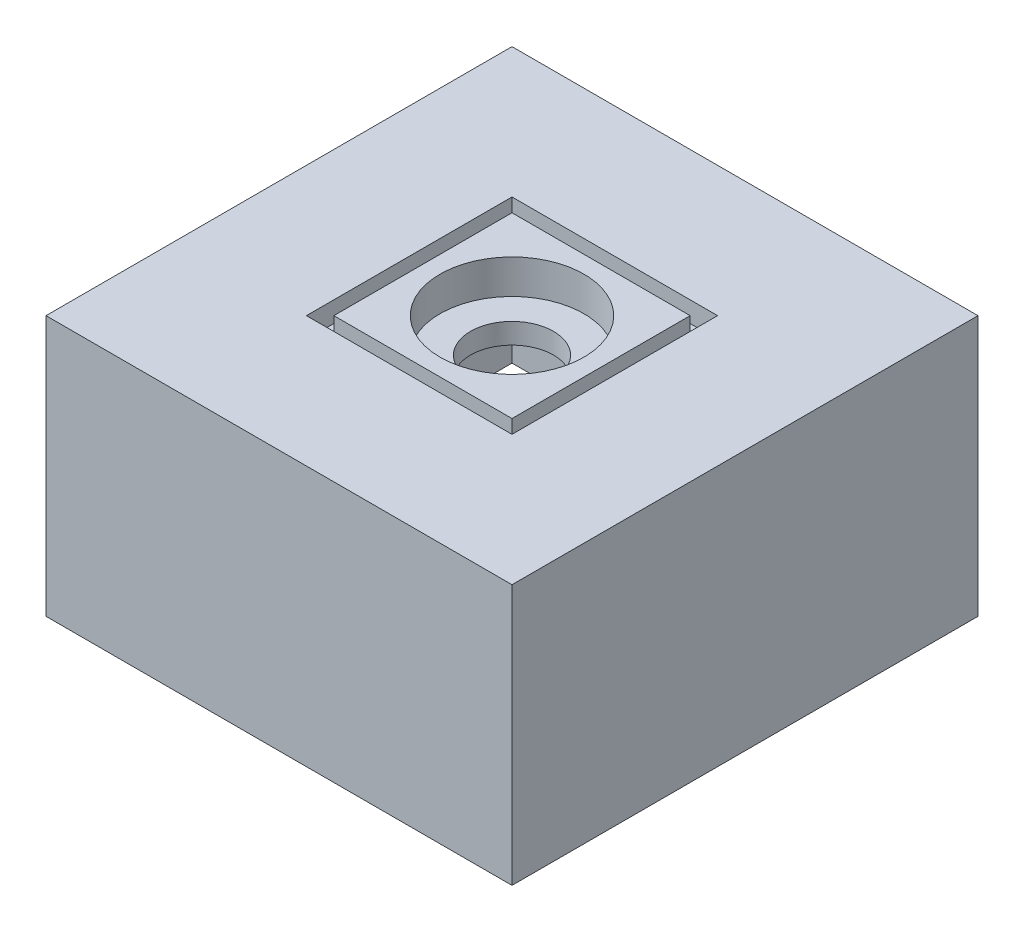
SolidWorks part; units mm, degrees
ref_plane "Front Plane" through (0, 0, 0) normal (0, 0, 1) x (1, 0, 0)
ref_plane "Top Plane" through (0, 0, 0) normal (0, 1, 0) x (1, 0, 0)
ref_plane "Right Plane" through (0, 0, 0) normal (1, 0, 0) x (0, 0, -1)
sketch "Sketch2" plane through (0, 0, 0) normal (0, 1, 0) x (1, 0, 0)
  line L1 (0, 0) -> (68, 0)
  line L2 (0, 0) -> (0, -68)
  line L3 (0, -68) -> (68, -68)
  line L4 (68, 0) -> (68, -68)
  dimension "D1" = 68
  dimension "D2" = 68
extrude "Boss-Extrude1" add sketch "Sketch2" along normal blind 38
sketch "Sketch3" plane through (0, 0, 0) normal (0, -1, 0) x (1, 0, 0)
  line L0 (0, 68) -> (68, 68) construction
  line L1 (2, 66) -> (66, 66)
  line L2 (2, 66) -> (2, 2)
  line L3 (2, 2) -> (66, 2)
  line L4 (66, 66) -> (66, 2)
  line L5 (0, 0) -> (0, 68) construction
  dimension "D1" = 64
  dimension "D2" = 2
  dimension "D3" = 2
extrude "Cut-Extrude1" cut sketch "Sketch3" against normal blind 30
sketch "Sketch5" plane through (0, 38, 0) normal (0, 1, 0) x (1, 0, 0)
  line L0 (0, 0) -> (68, -68) construction
  line L1 (0, -68) -> (68, 0) construction
  line L3 (19, -19) -> (49, -19)
  line L4 (19, -19) -> (19, -49)
  line L5 (19, -49) -> (49, -49)
  line L6 (49, -19) -> (49, -49)
  line L7 (21, -21) -> (47, -21)
  line L8 (21, -21) -> (21, -47)
  line L9 (21, -47) -> (47, -47)
  line L10 (47, -21) -> (47, -47)
  point P8 (34, -34)
  dimension "D1" = 30
  dimension "D2" = 26
extrude "Cut-Extrude2" cut sketch "Sketch5" against normal blind 3
sketch "Sketch6" plane through (0, 38, 0) normal (0, 1, 0) x (1, 0, 0)
  line L0 (47, -21) -> (21, -21) construction
  line L3 (47, -47) -> (47, -21) construction
  circle A0 centre (34, -34) radius 6.05
  dimension "D3" = 12.1
  dimension "D1" = 13
  dimension "D2" = 13
extrude "Cut-Extrude3" cut sketch "Sketch6" against normal through all
sketch "Sketch7" plane through (0, 38, 0) normal (0, 1, 0) x (1, 0, 0)
  circle A0 centre (34, -34) radius 10.5
  dimension "D1" = 21
extrude "Cut-Extrude4" cut sketch "Sketch7" against normal blind 5
sketch "Sketch8" plane through (0, 0, 2) normal (0, 0, 1) x (1, 0, 0)
  line L0 (2, 30) -> (66, 30) construction
  line L1 (66, 30) -> (66, 0) construction
  circle A0 centre (56, 5) radius 1.5
  dimension "D1" = 3
  dimension "D2" = 25
  dimension "D3" = 10
extrude "Cut-Extrude5" cut sketch "Sketch8" against normal through all
sketch "Sketch9" plane through (0, 30, 0) normal (0, -1, 0) x (1, 0, 0)
  line L0 (66, 66) -> (2, 66) construction
  line L1 (2, 66) -> (2, 2) construction
  circle A0 centre (10, 58) radius 2.5
  dimension "D1" = 5
  dimension "D2" = 8
  dimension "D3" = 8
extrude "Boss-Extrude2" add sketch "Sketch9" along normal blind 7.5
sketch "Sketch10" plane through (0, 22.5, 0) normal (0, -1, 0) x (1, 0, 0)
  circle A0 centre (10, 58) radius 1.5
  dimension "D1" = 3
extrude "Boss-Extrude3" add sketch "Sketch10" along normal blind 2
sketch "Sketch11" plane through (0, 20.5, 0) normal (0, -1, 0) x (1, 0, 0)
  circle A0 centre (10, 58) radius 2.5
  dimension "D1" = 5
extrude "Boss-Extrude4" add sketch "Sketch11" along normal blind 2
